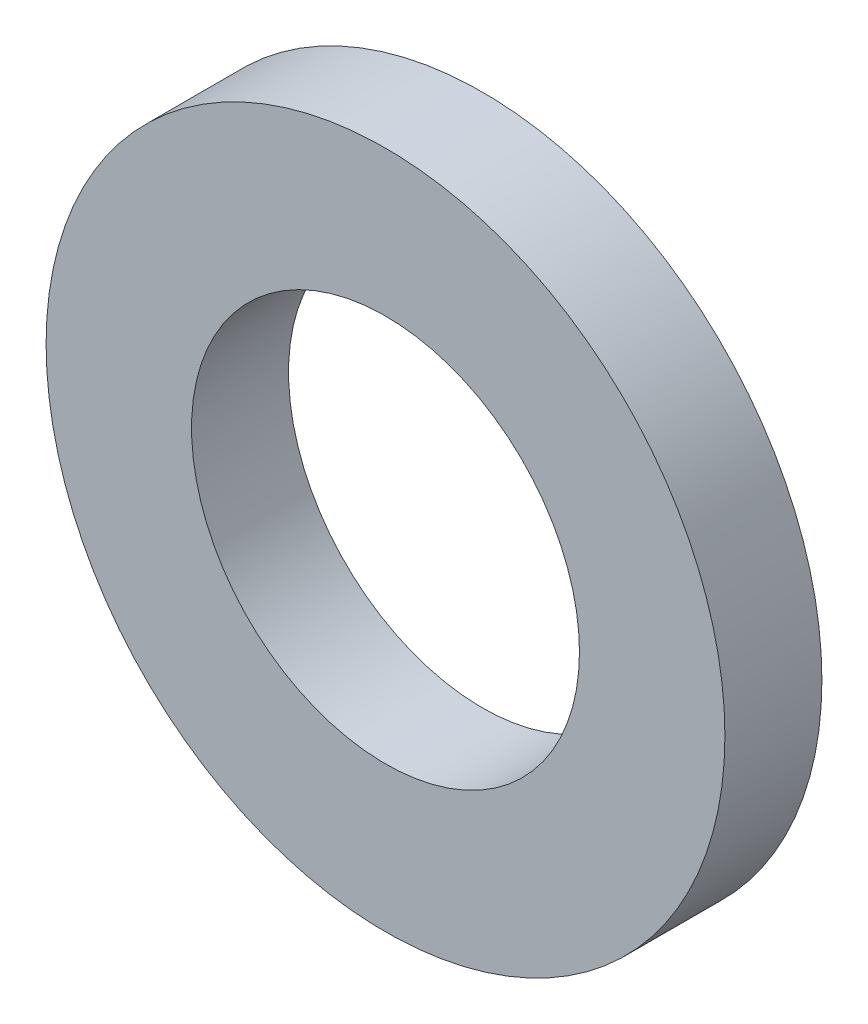
SolidWorks part; units mm, degrees
ref_plane "Plan de face" through (0, 0, 0) normal (0, 0, 1) x (1, 0, 0)
ref_plane "Plan de dessus" through (0, 0, 0) normal (0, 1, 0) x (1, 0, 0)
ref_plane "Plan de droite" through (0, 0, 0) normal (1, 0, 0) x (0, 0, -1)
sketch "Esquisse1" plane through (0, 0, 0) normal (0, 0, 1) x (1, 0, 0)
  circle A0 centre (0, 0) radius 2
  circle A1 centre (0, 0) radius 3.5
  dimension "D1" = 4
  dimension "D2" = 7
extrude "Boss.-Extru.1" add sketch "Esquisse1" along normal blind 1
